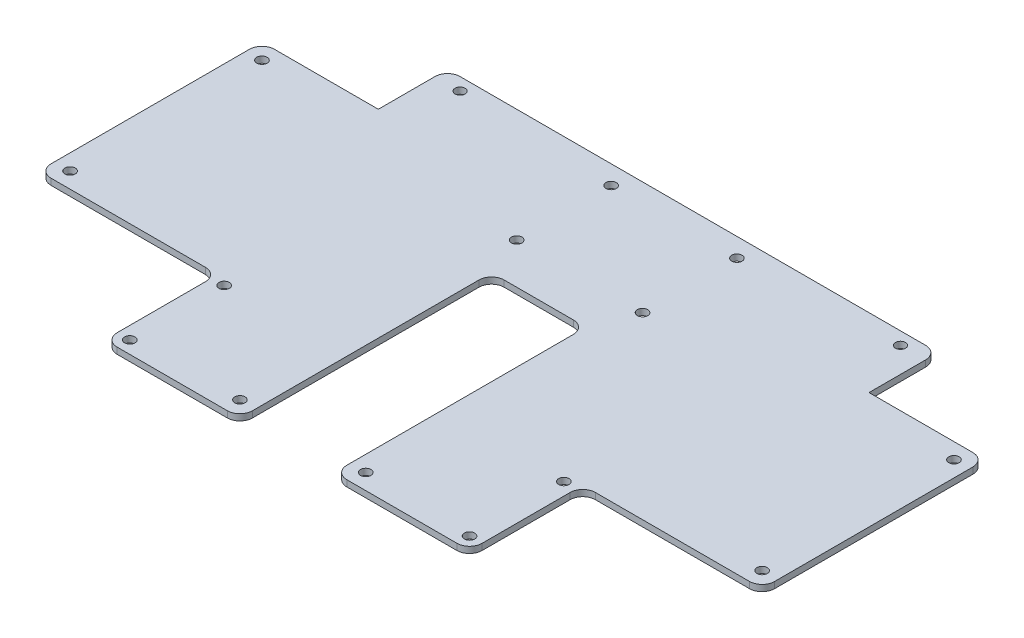
SolidWorks part; units mm, degrees
material "ABS PC"
ref_plane "Front Plane" through (0, 0, 0) normal (0, 0, 1) x (1, 0, 0)
ref_plane "Top Plane" through (0, 0, 0) normal (0, 1, 0) x (1, 0, 0)
ref_plane "Right Plane" through (0, 0, 0) normal (1, 0, 0) x (0, 0, -1)
sketch "Sketch1" plane through (0, 0, 0) normal (0, 1, 0) x (1, 0, 0)
  line L1 (0, 0) -> (230, 0)
  line L2 (0, 0) -> (0, 129)
  line L3 (0, 129) -> (230, 129)
  line L4 (230, 0) -> (230, 129)
  dimension "D1" = 230
  dimension "D2" = 129
extrude "Boss-Extrude1" add sketch "Sketch1" along normal blind 2
sketch "Sketch2" plane through (0, 2, 0) normal (0, 1, 0) x (1, 0, 0)
  line L1 (0, 129) -> (37, 129)
  line L2 (0, 129) -> (0, 107)
  line L3 (0, 107) -> (37, 107)
  line L4 (37, 129) -> (37, 107)
  line L5 (0, 0) -> (57, 0)
  line L6 (0, 0) -> (0, 36)
  line L7 (0, 36) -> (57, 36)
  line L8 (57, 0) -> (57, 36)
  line L9 (230, 129) -> (193, 129)
  line L10 (230, 129) -> (230, 107)
  line L11 (230, 107) -> (193, 107)
  line L12 (193, 129) -> (193, 107)
  line L13 (230, 0) -> (173, 0)
  line L14 (230, 0) -> (230, 36)
  line L15 (230, 36) -> (173, 36)
  line L16 (173, 0) -> (173, 36)
  line L17 (100, 0) -> (130, 0)
  line L18 (100, 0) -> (100, 80)
  line L19 (100, 80) -> (130, 80)
  line L20 (130, 0) -> (130, 80)
  dimension "D1" = 37
  dimension "D2" = 22
  dimension "D3" = 36
  dimension "D4" = 37
  dimension "D5" = 57
  dimension "D6" = 57
  dimension "D7" = 36
  dimension "D8" = 22
  dimension "D9" = 100
  dimension "D10" = 100
  dimension "D11" = 80
extrude "Cut-Extrude1" cut sketch "Sketch2" against normal through all
sketch "Sketch3" plane through (0, 0, 0) normal (0, -1, 0) x (1, 0, 0)
  line L0 (57, -36) -> (0, -36) construction
  line L1 (0, -107) -> (0, -36) construction
  line L2 (0, -107) -> (37, -107) construction
  line L3 (57, 0) -> (100, 0) construction
  line L4 (100, -80) -> (100, 0) construction
  line L5 (193, -129) -> (37, -129) construction
  line L6 (115, -80) -> (115, -129) construction
  line L7 (130, -80) -> (100, -80) construction
  line L8 (57, 0) -> (57, -36) construction
  line L9 (37, -107) -> (37, -129) construction
  circle A0 centre (5, -41) radius 1.65
  circle A1 centre (5, -102) radius 1.65
  circle A2 centre (95, -5) radius 1.65
  circle A3 centre (95, -93) radius 1.65
  circle A4 centre (95, -123) radius 1.65
  circle A5 centre (135, -93) radius 1.65
  circle A6 centre (135, -5) radius 1.65
  circle A7 centre (135, -123) radius 1.65
  circle A8 centre (225, -41) radius 1.65
  circle A9 centre (225, -102) radius 1.65
  circle A14 centre (61, -34) radius 1.65
  circle A15 centre (61, -4) radius 1.65
  circle A16 centre (169, -34) radius 1.65
  circle A17 centre (169, -4) radius 1.65
  circle A18 centre (45, -125) radius 1.6
  circle A19 centre (185, -125) radius 1.6
  dimension "D1" = 3.3
  dimension "D6" = 3.3
  dimension "D7" = 3.3
  dimension "D11" = 3.3
  dimension "D13" = 3.3
  dimension "D15" = 4
  dimension "D16" = 2
  dimension "D14" = 3.3
  dimension "D17" = 30
  dimension "D18" = 3.3
  dimension "D23" = 3.2
  dimension "D2" = 5
  dimension "D3" = 5
  dimension "D4" = 5
  dimension "D5" = 5
  dimension "D8" = 5
  dimension "D9" = 5
  dimension "D10" = 30
  dimension "D12" = 6
  dimension "D19" = 4
  dimension "D20" = 20
  dimension "D21" = 20
  dimension "D22" = 4
  dimension "D24" = 8
extrude "Cut-Extrude2" cut sketch "Sketch3" against normal blind 10
fillet "Fillet1" radius 4 14 edges at (100, 1, 0) (130, 1, 0) (230, 1, -36) (230, 1, -107) (0, 1, -36) (0, 1, -107) (130, 1, -80) (100, 1, -80) (193, 1, -129) (37, 1, -129) (173, 1, -36) (173, 1, 0) (57, 1, -36) (57, 1, 0)
